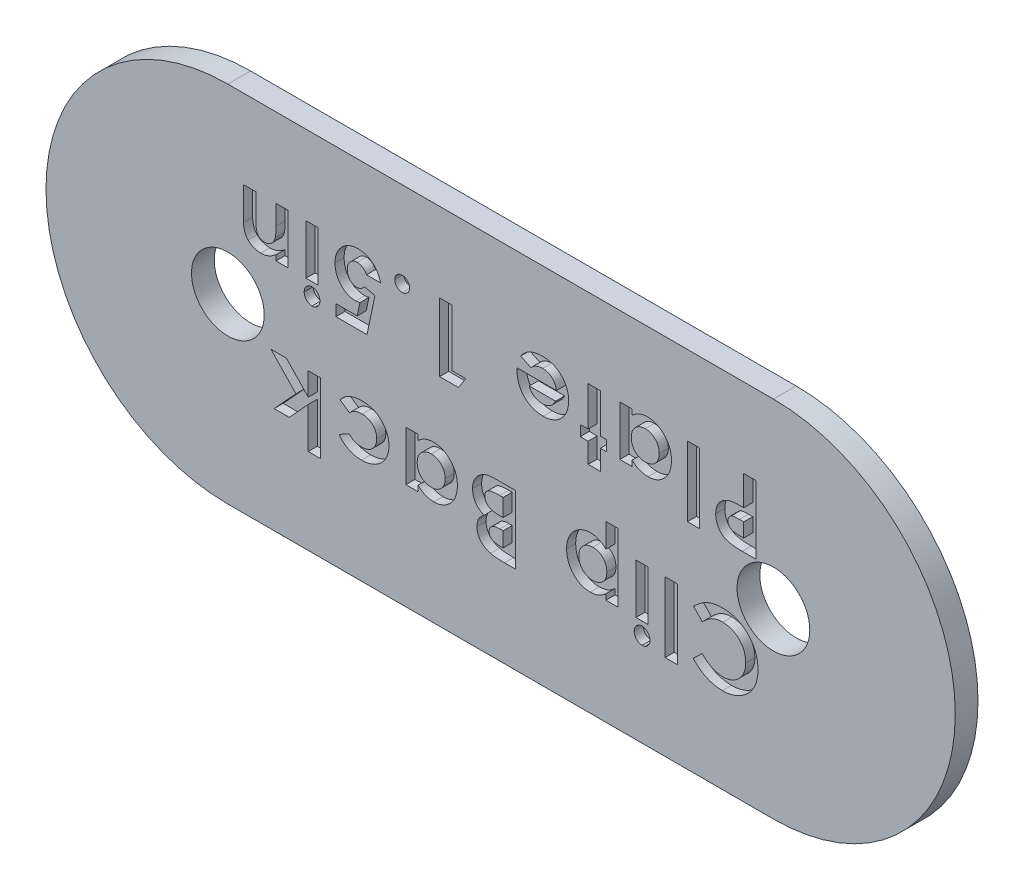
SolidWorks part; units mm, degrees
ref_plane "Front Plane" through (0, 0, 0) normal (0, 0, 1) x (1, 0, 0)
ref_plane "Top Plane" through (0, 0, 0) normal (0, 1, 0) x (1, 0, 0)
ref_plane "Right Plane" through (0, 0, 0) normal (1, 0, 0) x (0, 0, -1)
sketch "Sketch1" plane through (0, 0, 0) normal (0, 0, 1) x (1, 0, 0)
  line L0 (-19.05, 0) -> (19.05, 0) construction
  line L1 (-19.05, 12.7) -> (19.05, 12.7)
  line L2 (-19.05, -12.7) -> (19.05, -12.7)
  arc A0 (-19.05, 12.7) -> (-19.05, -12.7) centre (-19.05, 0) ccw
  arc A1 (19.05, -12.7) -> (19.05, 12.7) centre (19.05, 0) ccw
  circle A2 centre (19.05, 0) radius 2.54 construction
  circle A3 centre (-19.05, 0) radius 2.54 construction
  circle A4 centre (19.05, 0) radius 2.54
  circle A5 centre (-19.05, 0) radius 2.54
  point P4 (0, 0)
  dimension "D1" = 12.7
extrude "Boss-Extrude1" add sketch "Sketch1" along normal blind 1.5875
sketch "Sketch2" plane through (0, 0, 1.5875) normal (0, 0, 1) x (1, 0, 0)
  line L0 (23.3505, -1.8327) -> (-23.3505, -1.8327) construction
  text T0 "<b>Clip Back </b>\r\n<b>Plate 1.5in</b>" font "Century Gothic" height 4.7625
  point P3 (0, 0)
  point P4 (0, -2.4865)
  point P5 (19.5712, -0.6063)
  point P6 (0, -1.8327)
  point P7 (27.0846, -1.8327)
  point P8 (0, 0)
extrude "Cut-Extrude1" cut sketch "Sketch2" against normal blind 0.635
